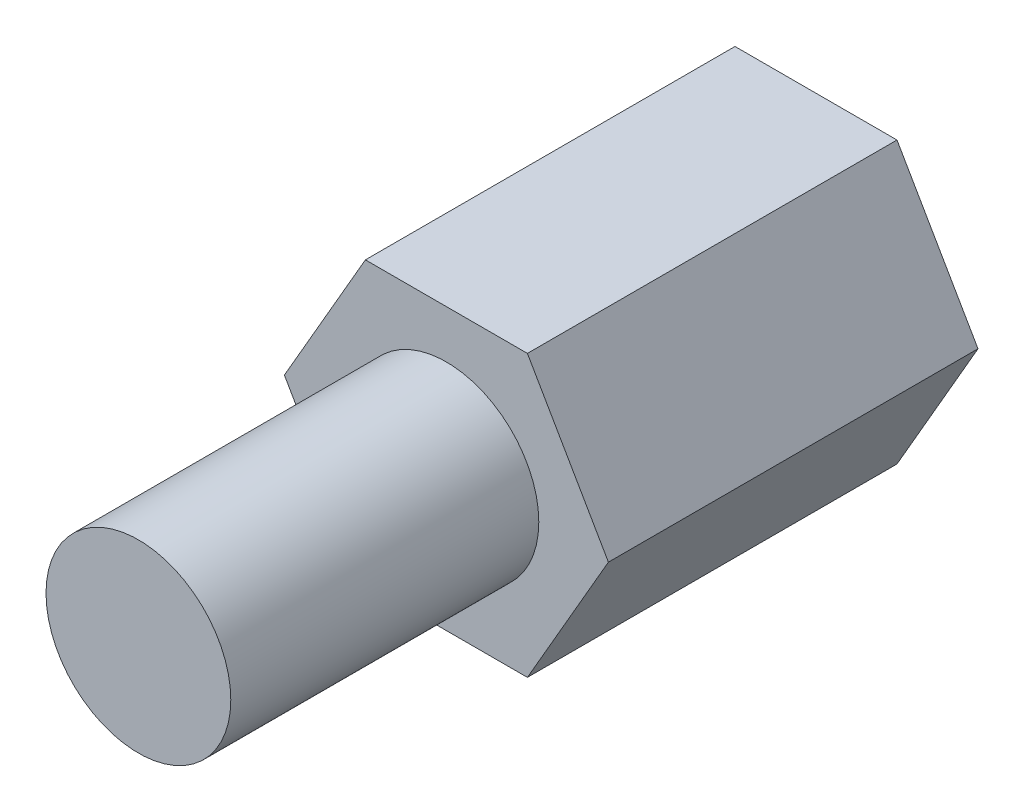
SolidWorks part; units mm, degrees
material "黃銅"
ref_plane "前基準面" through (0, 0, 0) normal (0, 0, 1) x (1, 0, 0)
ref_plane "上基準面" through (0, 0, 0) normal (0, 1, 0) x (1, 0, 0)
ref_plane "右基準面" through (0, 0, 0) normal (1, 0, 0) x (0, 0, -1)
sketch "草圖1" plane through (0, 0, 0) normal (0, 0, 1) x (1, 0, 0)
  line L1 (2.63, 0) -> (1.315, 2.2776)
  line L2 (1.315, 2.2776) -> (-1.315, 2.2776)
  line L3 (-1.315, 2.2776) -> (-2.63, 0)
  line L4 (-2.63, 0) -> (-1.315, -2.2776)
  line L5 (-1.315, -2.2776) -> (1.315, -2.2776)
  line L6 (1.315, -2.2776) -> (2.63, 0)
  circle A0 centre (0, 0) radius 2.2776 construction
  point P1 (2.5199, -0.753)
  dimension "D1" = 5.26
extrude "填料-伸長1" add sketch "草圖1" along normal blind 6
hole_wizard "M3x0.5 螺紋孔1" positions "草圖3" profile "草圖4" tap size "M3x0.5" standard "Ansi Metric"
sketch "草圖3" plane through (0, 0, 0) normal (0, 0, -1) x (-1, 0, 0)
  point P0 (0, 0)
sketch "草圖4" plane through (0, 0, 0) normal (1, 0, 0) x (0, 1, 0)
  line L0 (0, 0) -> (0, 4.7511)
  line L1 (0, 4.7511) -> (1.25, 4)
  line L2 (1.25, 4) -> (1.25, 0)
  line L5 (1.25, 0) -> (0, 0)
  line L10 (0, 4.7511) -> (-1.25, 4) construction
  line L11 (0, -6.35) -> (0, 107.95) construction
  dimension "螺孔鑽直徑" = 2.5
  dimension "螺孔鑽深度" = 4
  dimension "導頭角度" = 118
cosmetic thread "鑽孔螺紋1" parameters "D1"=4, "D2"=3
sketch "草圖5" plane through (0, 0, 6) normal (0, 0, 1) x (1, 0, 0)
  circle A0 centre (0, 0) radius 1.5
  dimension "D1" = 3
extrude "填料-伸長2" add sketch "草圖5" along normal blind 5
